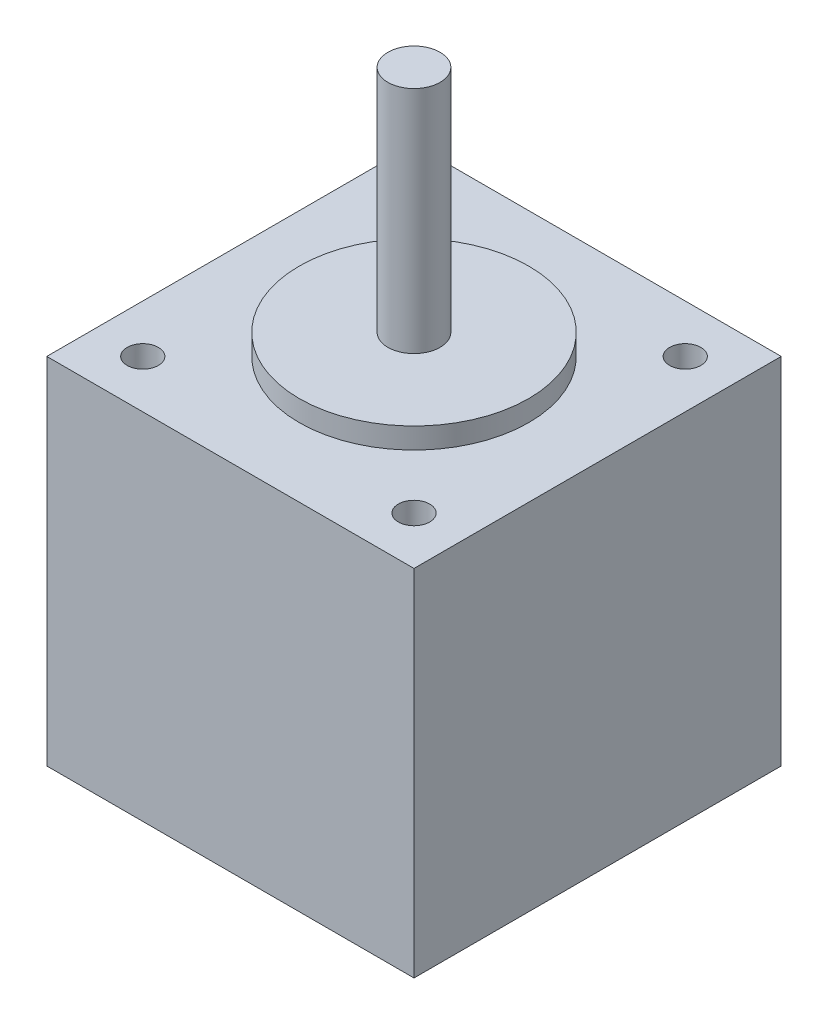
SolidWorks part; units mm, degrees
ref_plane "Front Plane" through (0, 0, 0) normal (0, 0, 1) x (1, 0, 0)
ref_plane "Top Plane" through (0, 0, 0) normal (0, 1, 0) x (1, 0, 0)
ref_plane "Right Plane" through (0, 0, 0) normal (1, 0, 0) x (0, 0, -1)
sketch "Sketch1" plane through (0, 0, 0) normal (0, 1, 0) x (1, 0, 0)
  line L1 (-17.6, -17.6) -> (17.6, -17.6)
  line L2 (-17.6, -17.6) -> (-17.6, 17.6)
  line L3 (-17.6, 17.6) -> (17.6, 17.6)
  line L4 (17.6, -17.6) -> (17.6, 17.6)
  line L5 (-17.6, -17.6) -> (17.6, 17.6) construction
  line L6 (-17.6, 17.6) -> (17.6, -17.6) construction
  point P0 (0, 0)
  dimension "D1" = 35.2
extrude "Boss-Extrude1" add sketch "Sketch1" along normal blind 34
sketch "Sketch2" plane through (0, 34, 0) normal (0, 1, 0) x (1, 0, 0)
  line L0 (-13, 13) -> (13, 13) construction
  line L1 (0, 0) -> (51.5186, 0) construction
  circle A0 centre (-13, 13) radius 1.5
  circle A1 centre (13, 13) radius 1.5
  point P0 (-13, 13)
  point P1 (13, 13)
  point P9 (0, 0)
  point P10 (0, 13)
  dimension "D2" = 3
  dimension "D1" = 26
  dimension "D3" = 13
extrude "Cut-Extrude1" cut sketch "Sketch2" against normal blind 4.5
mirror "Mirror1" about plane through (0, 0, 0) normal (0, 0, 1) of "Cut-Extrude1"
sketch "Sketch3" plane through (0, 34, 0) normal (0, 1, 0) x (1, 0, 0)
  circle A0 centre (0, 0) radius 11
  dimension "D1" = 22
extrude "Boss-Extrude2" add sketch "Sketch3" along normal blind 2
sketch "Sketch4" plane through (0, 36, 0) normal (0, 1, 0) x (1, 0, 0)
  circle A0 centre (0, 0) radius 2.5
  dimension "D1" = 5
extrude "Boss-Extrude3" add sketch "Sketch4" along normal blind 22
